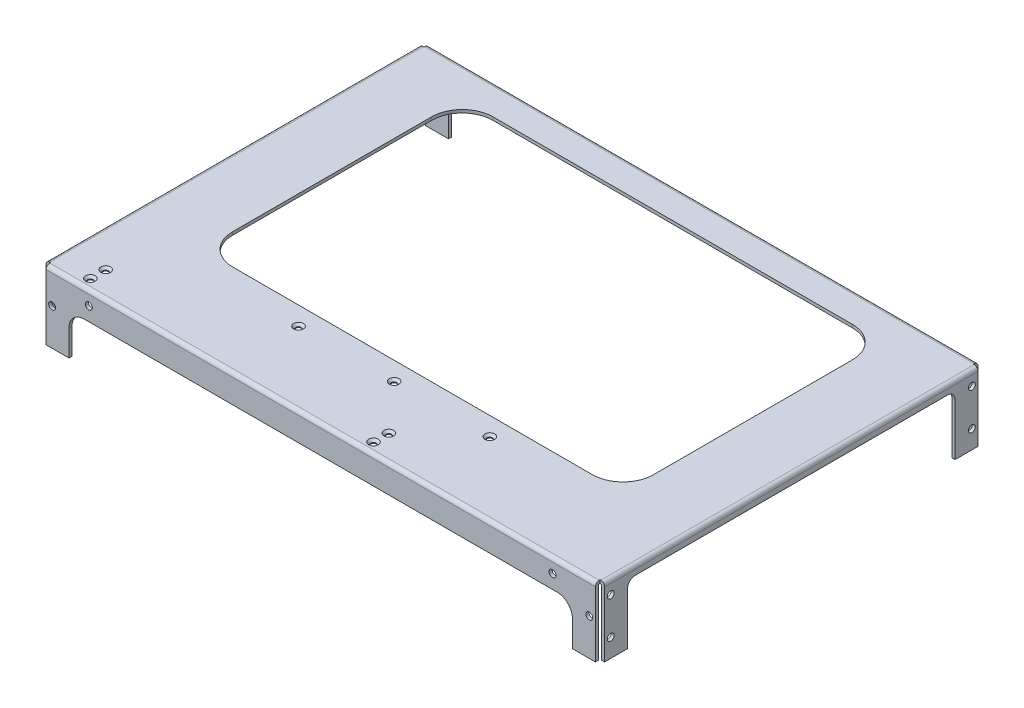
SolidWorks part; units mm, degrees
material "6061-T6 (SS)"
ref_plane "Front Plane" through (0, 0, 0) normal (0, 0, 1) x (1, 0, 0)
ref_plane "Top Plane" through (0, 0, 0) normal (0, 1, 0) x (1, 0, 0)
ref_plane "Right Plane" through (0, 0, 0) normal (1, 0, 0) x (0, 0, -1)
sketch "Sketch1" plane through (0, 0, 0) normal (1, 0, 0) x (0, 0, -1)
  line L0 (123, -45) -> (125, -45)
  line L1 (-122.5, 0) -> (122.5, 0)
  line L2 (-125, -2.5) -> (-125, -45)
  line L3 (-125, -45) -> (-123, -45)
  line L4 (125, -2.5) -> (125, -45)
  line L6 (-123, -45) -> (-123, -2.5)
  line L7 (-122.5, -2) -> (122.5, -2)
  line L8 (123, -45) -> (123, -2.5)
  arc A0 (-122.5, 0) -> (-125, -2.5) centre (-122.5, -2.5) ccw
  arc A1 (122.5, 0) -> (125, -2.5) centre (122.5, -2.5) cw
  arc A2 (122.5, -2) -> (123, -2.5) centre (122.5, -2.5) cw
  arc A3 (-123, -2.5) -> (-122.5, -2) centre (-122.5, -2.5) cw
  dimension "D1" = 2.5
  dimension "D2" = 250
  dimension "D3" = 2
  dimension "D4" = 45
extrude "Boss-Extrude1" add sketch "Sketch1" along normal mid plane 365
sketch "Sketch2" plane through (0, 0, 125) normal (0, 0, 1) x (1, 0, 0)
  line L0 (182.5, -45) -> (-182.5, -45) construction
  line L1 (-164.5, -45) -> (164.5, -45)
  line L2 (-164.5, -45) -> (-164.5, -28)
  line L3 (-154.5, -18) -> (154.5, -18)
  line L4 (164.5, -45) -> (164.5, -28)
  line L5 (182.5, 0) -> (-182.5, 0) construction
  line L6 (-182.5, -2.5) -> (-182.5, -45) construction
  line L7 (182.5, -2.5) -> (182.5, -45) construction
  arc A0 (154.5, -18) -> (164.5, -28) centre (154.5, -28) cw
  arc A1 (-164.5, -28) -> (-154.5, -18) centre (-154.5, -28) cw
  dimension "D4" = 10
  dimension "D1" = 18
  dimension "D2" = 18
  dimension "D3" = 18
extrude "Cut-Extrude1" cut sketch "Sketch2" against normal through all
sketch "Sketch3" plane through (0, 0, 0) normal (0, 1, 0) x (1, 0, 0)
  line L0 (-182.5, 122.5) -> (-182.5, -122.5) construction
  line L1 (-117.5, 105) -> (117.5, 105)
  line L2 (-137.5, 85) -> (-137.5, -45)
  line L3 (-117.5, -65) -> (117.5, -65)
  line L4 (137.5, 85) -> (137.5, -45)
  line L5 (182.5, 122.5) -> (182.5, -122.5) construction
  line L6 (182.5, 125) -> (-182.5, 125) construction
  line L7 (182.5, -125) -> (-182.5, -125) construction
  arc A0 (117.5, 105) -> (137.5, 85) centre (117.5, 85) cw
  arc A1 (137.5, -45) -> (117.5, -65) centre (117.5, -45) cw
  arc A2 (-137.5, -45) -> (-117.5, -65) centre (-117.5, -45) ccw
  arc A3 (-117.5, 105) -> (-137.5, 85) centre (-117.5, 85) ccw
  dimension "D1" = 20
  dimension "D2" = 45
  dimension "D3" = 45
  dimension "D4" = 20
  dimension "D5" = 60
extrude "Cut-Extrude2" cut sketch "Sketch3" against normal blind 10
sketch "Sketch4" plane through (0, -2, 0) normal (0, -1, 0) x (1, 0, 0)
  line L0 (182.5, -123) -> (-182.5, -123) construction
  line L1 (-182.5, 123) -> (-180.5, 123)
  line L2 (-182.5, 123) -> (-182.5, -123)
  line L3 (-182.5, -123) -> (-180.5, -123)
  line L4 (-180.5, 123) -> (-180.5, -123)
  line L5 (182.5, 123) -> (164.5, 123) construction
  line L6 (182.5, -123) -> (180.5, -123)
  line L7 (182.5, -123) -> (182.5, 123)
  line L8 (182.5, 123) -> (180.5, 123)
  line L9 (180.5, -123) -> (180.5, 123)
  dimension "D1" = 2
extrude "Boss-Extrude2" add sketch "Sketch4" along normal up to surface (43 mm away) up to face at (-173.5, -45, 124)
sketch "Sketch5" plane through (0, -45, 0) normal (0, -1, 0) x (1, 0, 0)
  line L1 (-182.5, 125) -> (-179.5, 125)
  line L2 (-182.5, 125) -> (-182.5, 122)
  line L3 (-182.5, 122) -> (-179.5, 122)
  line L4 (-179.5, 125) -> (-179.5, 122)
  line L5 (-182.5, -125) -> (-179.5, -125)
  line L6 (-182.5, -125) -> (-182.5, -122)
  line L7 (-182.5, -122) -> (-179.5, -122)
  line L8 (-179.5, -125) -> (-179.5, -122)
  line L9 (182.5, -125) -> (179.5, -125)
  line L10 (182.5, -125) -> (182.5, -122)
  line L11 (182.5, -122) -> (179.5, -122)
  line L12 (179.5, -125) -> (179.5, -122)
  line L13 (182.5, 125) -> (179.5, 125)
  line L14 (182.5, 125) -> (182.5, 122)
  line L15 (182.5, 122) -> (179.5, 122)
  line L16 (179.5, 125) -> (179.5, 122)
  dimension "D1" = 3
extrude "Cut-Extrude3" cut sketch "Sketch5" against normal through all
fillet "Fillet1" radius 0.5 2 edges at (180.5, -2, 0) (-180.5, -2, 0)
fillet "Fillet2" radius 2.5 2 edges at (182.5, 0, 0) (-182.5, 0, 0)
sketch "Sketch8" plane through (-182.5, 0, 0) normal (-1, 0, 0) x (0, 0, 1)
  line L0 (122, -45) -> (-122, -45) construction
  line L1 (-107, -45) -> (107, -45)
  line L2 (-107, -45) -> (-107, -11)
  line L3 (-102, -6) -> (102, -6)
  line L4 (107, -45) -> (107, -11)
  line L5 (-125, -2.5) -> (-125, -45) construction
  line L6 (125, -45) -> (125, -28) construction
  line L7 (-122, 0) -> (122, 0) construction
  arc A0 (102, -6) -> (107, -11) centre (102, -11) cw
  arc A1 (-107, -11) -> (-102, -6) centre (-102, -11) cw
  dimension "D4" = 5
  dimension "D1" = 18
  dimension "D2" = 18
  dimension "D3" = 6
extrude "Cut-Extrude6" cut sketch "Sketch8" against normal through all
sketch "Sketch9" plane through (-182.5, 0, 0) normal (-1, 0, 0) x (0, 0, 1)
  circle A0 centre (-118, -9) radius 2.25
  circle A1 centre (-118, -33) radius 2.25
  circle A2 centre (118, -9) radius 2.25
  circle A3 centre (118, -33) radius 2.25
  dimension "D1" = 4.5
extrude "Cut-Extrude7" cut sketch "Sketch9" against normal through all
sketch "Sketch10" plane through (0, 0, 125) normal (0, 0, 1) x (1, 0, 0)
  circle A1 centre (-151.5, -9) radius 2.25
  circle A3 centre (175.5, -21) radius 2.25
  circle A4 centre (151.5, -9) radius 2.25
  circle A5 centre (-175.5, -21) radius 2.25
  dimension "D1" = 4.5
extrude "Cut-Extrude8" cut sketch "Sketch10" against normal blind 10
sketch "Sketch11" plane through (0, 0, -125) normal (0, 0, -1) x (-1, 0, 0)
  circle A0 centre (-175.5, -21) radius 2.25
  circle A2 centre (-151.5, -9) radius 2.25
  circle A3 centre (151.5, -9) radius 2.25
  circle A5 centre (175.5, -21) radius 2.25
  dimension "D1" = 4.5
extrude "Cut-Extrude9" cut sketch "Sketch11" against normal blind 10
sketch "Sketch12" plane through (0, 0, 0) normal (0, 1, 0) x (1, 0, 0)
  line L0 (-62.5, -65) -> (-62.5, -89) construction
  line L1 (62.5, -65) -> (62.5, -89) construction
  circle A0 centre (0, -77) radius 1.5
  circle A1 centre (62.5, -77) radius 1.5
  circle A2 centre (-62.5, -77) radius 1.5
  circle A3 centre (-157.5, -108) radius 1.5
  circle A4 centre (-157.5, -118) radius 1.5
  circle A5 centre (27.5, -108) radius 1.5
  circle A6 centre (27.5, -118) radius 1.5
  dimension "D1" = 3
extrude "Cut-Extrude10" cut sketch "Sketch12" against normal blind 10
hole_wizard "CSK for M3 Flat Head Machine Screw1" positions "Sketch14" profile "Sketch13" countersink size "M3" standard "Ansi Metric" end condition through all
sketch "Sketch14" plane through (0, 0, 0) normal (0, 1, 0) x (-1, 0, 0)
  point P0 (62.5, 77)
  point P1 (0, 77)
  point P4 (-62.5, 77)
  point P10 (157.5, 108)
  point P13 (157.5, 118)
  point P16 (-27.5, 108)
  point P19 (-27.5, 118)
sketch "Sketch13" plane through (-62.5, 0, 77) normal (1, 0, 0) x (0, 0, 1)
  line L0 (0, 0) -> (0, 45)
  line L1 (0, 45) -> (1.7, 45)
  line L2 (1.7, 45) -> (1.7, 1.45)
  line L3 (1.7, 1.45) -> (3.15, 0)
  line L5 (3.15, 0) -> (0, 0)
  line L6 (-1.7, 1.45) -> (-3.15, 0) construction
  line L11 (0, -6.35) -> (0, 107.95) construction
  dimension "Thru Hole Dia." = 3.4
  dimension "Thru Hole Depth" = 45
  dimension "Near C'Sink Dia." = 6.3
  dimension "Near C'Sink Angle" = 90
